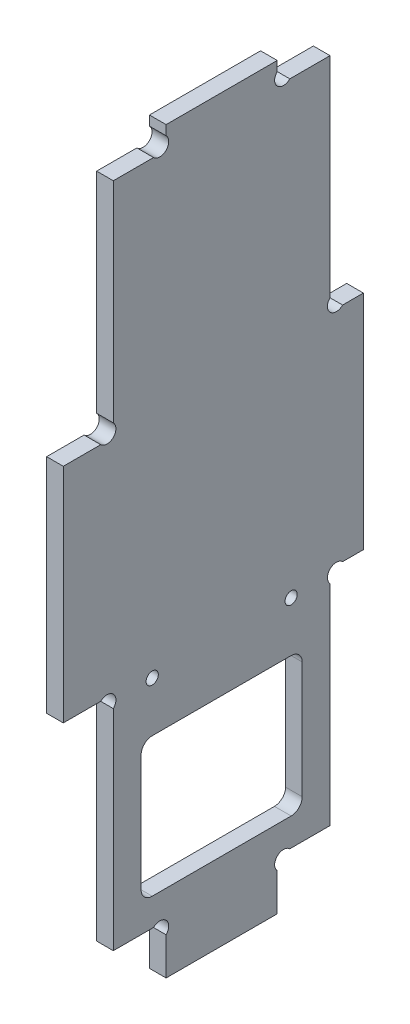
SolidWorks part; units mm, degrees
ref_plane "Plan de face" through (0, 0, 0) normal (0, 0, 1) x (1, 0, 0)
ref_plane "Plan de dessus" through (0, 0, 0) normal (0, 1, 0) x (1, 0, 0)
ref_plane "Plan de droite" through (0, 0, 0) normal (1, 0, 0) x (0, 0, -1)
sketch "Esquisse1" plane through (0, 0, 0) normal (1, 0, 0) x (0, 0, -1)
  line L13 (18.5, 6.7373) -> (18.5, 0)
  line L15 (16.2373, 9) -> (9, 9)
  line L17 (50.2627, 49) -> (54, 49)
  line L18 (6.7373, 49) -> (0, 49)
  line L19 (38.5, 6.7373) -> (38.5, 0)
  line L20 (50.2627, 89) -> (54, 89)
  line L21 (6.7373, 89) -> (0, 89)
  line L22 (18.5, 0) -> (38.5, 0)
  line L23 (40.7627, 9) -> (48, 9)
  line L24 (48, 9) -> (48, 46.7373)
  line L25 (9, 9) -> (9, 46.7373)
  line L26 (54, 89) -> (54, 49)
  line L27 (0, 49) -> (0, 89)
  line L29 (18.5, 131.2627) -> (18.5, 133)
  line L30 (38.5, 131.2627) -> (38.5, 133)
  line L31 (9, 91.2627) -> (9, 129)
  line L32 (9, 129) -> (16.2373, 129)
  line L33 (18.5, 133) -> (38.5, 133)
  line L34 (40.7627, 129) -> (48, 129)
  line L35 (48, 129) -> (48, 91.2627)
  arc A0 (50.2627, 49) -> (48, 46.7373) centre (49.1314, 47.8686) ccw
  arc A1 (9, 46.7373) -> (6.7373, 49) centre (7.8686, 47.8686) ccw
  arc A2 (18.5, 6.7373) -> (16.2373, 9) centre (17.3686, 7.8686) ccw
  arc A3 (38.5, 6.7373) -> (40.7627, 9) centre (39.6314, 7.8686) cw
  arc A4 (9, 91.2627) -> (6.7373, 89) centre (7.8686, 90.1314) cw
  arc A5 (50.2627, 89) -> (48, 91.2627) centre (49.1314, 90.1314) cw
  arc A6 (16.2373, 129) -> (18.5, 131.2627) centre (17.3686, 130.1314) ccw
  arc A7 (40.7627, 129) -> (38.5, 131.2627) centre (39.6314, 130.1314) cw
  point P1 (12.6186, 9)
  dimension "D14" = 1.1314
  dimension "D15" = 1.1314
  dimension "D17" = 1.1314
  dimension "D23" = 1.1314
  dimension "D10" = 1.6
  dimension "D1" = 6
  dimension "D2" = 9
  dimension "D3" = 9.5
  dimension "D4" = 9.5
  dimension "D5" = 9
  dimension "D6" = 40
  dimension "D7" = 40
  dimension "D8" = 40
  dimension "D9" = 4
  dimension "D11" = 1.1314
  dimension "D12" = 1.1314
  dimension "D13" = 1.1314
  dimension "D16" = 20
  dimension "D18" = 1.1314
  dimension "D19" = 1.1314
  dimension "D20" = 1.1314
  dimension "D21" = 1.1314
  dimension "D22" = 1.1314
  dimension "D24" = 3.7373
  dimension "D25" = 1.7373
  dimension "D26" = 1.1314
  dimension "D27" = 7.2373
  dimension "D28" = 1.1314
  dimension "D29" = 1.7373
  dimension "D30" = 20
  dimension "D31" = 39
  dimension "D32" = 39
extrude "Extrusion1" add sketch "Esquisse1" along normal blind 3
sketch "Esquisse2" plane through (3, 0, 0) normal (1, 0, 0) x (0, 0, -1)
  line L0 (9, 46.7373) -> (9, 9) construction
  line L1 (14, 14) -> (43, 14)
  line L2 (14, 14) -> (14, 39)
  line L3 (14, 39) -> (43, 39)
  line L4 (43, 14) -> (43, 39)
  line L5 (48, 9) -> (48, 46.7373) construction
  line L6 (9, 9) -> (16.2373, 9) construction
  dimension "D1" = 5
  dimension "D2" = 5
  dimension "D3" = 5
  dimension "D4" = 25
extrude "Enlèv. mat.-Extru.1" cut sketch "Esquisse2" against normal through all
fillet "Congé1" radius 2 4 edges at (1.5, 14, -43) (1.5, 14, -14) (1.5, 39, -14) (1.5, 39, -43)
sketch "Esquisse3" plane through (3, 0, 0) normal (1, 0, 0) x (0, 0, -1)
  line L0 (41, 39) -> (16, 39) construction
  line L1 (14, 37) -> (14, 16) construction
  line L2 (43, 16) -> (43, 37) construction
  circle A0 centre (16, 48) radius 1.1
  circle A1 centre (41, 48) radius 1.1
  dimension "D2" = 2.2
  dimension "D1" = 9
  dimension "D3" = 2
  dimension "D4" = 2
  dimension "D5" = 25
extrude "Enlèv. mat.-Extru.2" cut sketch "Esquisse3" against normal through all
